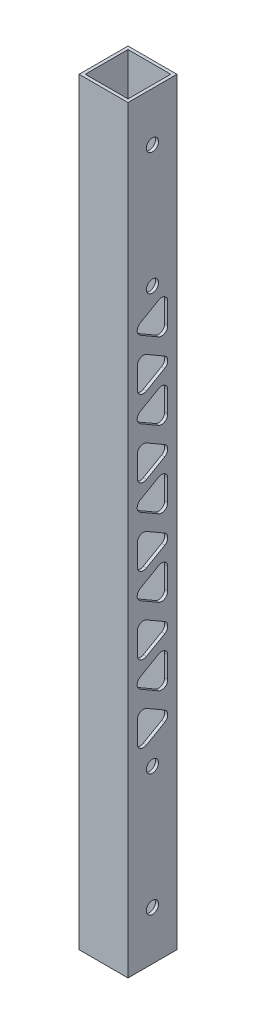
SolidWorks part; units mm, degrees
material "6061 Alloy"
ref_plane "Front Plane" through (0, 0, 0) normal (0, 0, 1) x (1, 0, 0)
ref_plane "Top Plane" through (0, 0, 0) normal (0, 1, 0) x (1, 0, 0)
ref_plane "Right Plane" through (0, 0, 0) normal (1, 0, 0) x (0, 0, -1)
sketch "Sketch1" plane through (0, 0, 0) normal (0, 1, 0) x (1, 0, 0)
  line L0 (-25.4, -25.4) -> (25.4, 25.4) construction
  line L1 (-25.4, 25.4) -> (25.4, 25.4)
  line L2 (-25.4, 25.4) -> (-25.4, -25.4)
  line L3 (-25.4, -25.4) -> (25.4, -25.4)
  line L4 (25.4, 25.4) -> (25.4, -25.4)
  line L5 (22.225, -22.225) -> (-22.225, 22.225) construction
  line L6 (-22.225, 22.225) -> (22.1918, 22.225)
  line L7 (-22.225, 22.225) -> (-22.225, -22.1918)
  line L8 (-22.225, -22.1918) -> (22.1918, -22.1918)
  line L9 (22.1918, 22.225) -> (22.1918, -22.1918)
  point P7 (0, 0)
  point P10 (0, 0)
  point P14 (0, 0)
  dimension "D1" = 50.8
  dimension "D2" = 3.175
  dimension "D3" = 3.175
extrude "Boss-Extrude1" add sketch "Sketch1" along normal blind 787.4
sketch "Sketch2" plane through (-25.4, 0, 0) normal (-1, 0, 0) x (0, 0, 1)
  line L0 (25.4, 393.7) -> (-25.4, 393.7) construction
  line L1 (25.4, 787.4) -> (25.4, 0) construction
  line L2 (-25.4, 787.4) -> (-25.4, 0) construction
  line L3 (0, 50.8) -> (0, 736.6) construction
  line L4 (0, 609.6) -> (0, 177.8) construction
  circle A0 centre (0, 50.8) radius 6.35
  circle A1 centre (0, 177.8) radius 6.35
  circle A2 centre (0, 609.6) radius 6.35
  circle A3 centre (0, 736.6) radius 6.35
  point P10 (0, 393.7)
  point P13 (0, 393.7)
  dimension "D3" = 12.7
extrude "Cut-Extrude1" cut sketch "Sketch2" against normal through all
sketch "Sketch3" plane through (-25.4, 0, 0) normal (-1, 0, 0) x (0, 0, 1)
  line L0 (15.7359, 216.4425) -> (15.7359, 861.9822) construction
  line L1 (-12.7, 210.9432) -> (6.2109, 200.025)
  line L2 (15.7359, 205.5243) -> (15.7359, 227.3607)
  line L3 (6.2109, 232.86) -> (-12.7, 221.9417)
  line L4 (12.7, 264.382) -> (-6.35, 275.3805)
  line L5 (-15.875, 269.8813) -> (-15.875, 247.8842)
  line L6 (-6.35, 242.385) -> (12.7, 253.3835)
  line L7 (-25.4, 787.4) -> (-25.4, 0) construction
  line L8 (25.4, 787.4) -> (25.4, 0) construction
  line L9 (-25.4, 393.7) -> (25.4, 393.7) construction
  line L10 (-6.35, 177.8) -> (6.35, 177.8) construction
  line L11 (-12.7, 290.5293) -> (6.2109, 279.6111)
  line L12 (15.7359, 285.1104) -> (15.7359, 306.9468)
  line L13 (6.2109, 312.4461) -> (-12.7, 301.5279)
  line L14 (12.7, 343.9681) -> (-6.35, 354.9667)
  line L15 (-15.875, 349.4674) -> (-15.875, 327.4704)
  line L16 (-6.35, 321.9711) -> (12.7, 332.9696)
  line L17 (-12.7, 370.1155) -> (6.2109, 359.1972)
  line L18 (15.7359, 364.6965) -> (15.7359, 386.5329)
  line L19 (6.2109, 392.0322) -> (-12.7, 381.114)
  line L20 (12.7, 423.5542) -> (-6.35, 434.5528)
  line L21 (-15.875, 429.0535) -> (-15.875, 407.0565)
  line L22 (-6.35, 401.5572) -> (12.7, 412.5557)
  line L23 (-12.7, 449.7016) -> (6.2109, 438.7833)
  line L24 (15.7359, 444.2826) -> (15.7359, 466.1191)
  line L25 (6.2109, 471.6183) -> (-12.7, 460.7001)
  line L26 (12.7, 503.1404) -> (-6.35, 514.1389)
  line L27 (-15.875, 508.6396) -> (-15.875, 486.6426)
  line L28 (-6.35, 481.1433) -> (12.7, 492.1418)
  line L29 (-12.7, 529.2877) -> (6.2109, 518.3695)
  line L30 (15.7359, 523.8687) -> (15.7359, 545.7052)
  line L31 (6.2109, 551.2044) -> (-12.7, 540.2862)
  line L32 (12.7, 582.7265) -> (-6.35, 593.725)
  line L33 (-15.875, 588.2257) -> (-15.875, 566.2287)
  line L34 (-6.35, 560.7294) -> (12.7, 571.728)
  circle A0 centre (3.0823, 216.4425) radius 12.6536 construction
  circle A1 centre (-3.175, 258.8828) radius 12.7 construction
  arc A2 (-12.7, 210.9432) -> (-12.7, 221.9417) centre (-9.525, 216.4425) cw
  arc A3 (15.7359, 227.3607) -> (6.2109, 232.86) centre (9.3859, 227.3607) ccw
  arc A4 (6.2109, 200.025) -> (15.7359, 205.5243) centre (9.3859, 205.5243) ccw
  arc A5 (12.7, 264.382) -> (12.7, 253.3835) centre (9.525, 258.8828) cw
  arc A6 (-15.875, 247.8842) -> (-6.35, 242.385) centre (-9.525, 247.8842) ccw
  arc A7 (-6.35, 275.3805) -> (-15.875, 269.8813) centre (-9.525, 269.8813) ccw
  circle A11 centre (0, 177.8) radius 6.35 construction
  arc A12 (6.2109, 279.6111) -> (15.7359, 285.1104) centre (9.3859, 285.1104) ccw
  arc A13 (-12.7, 290.5293) -> (-12.7, 301.5279) centre (-9.525, 296.0286) cw
  arc A14 (15.7359, 306.9468) -> (6.2109, 312.4461) centre (9.3859, 306.9468) ccw
  arc A15 (-6.35, 354.9667) -> (-15.875, 349.4674) centre (-9.525, 349.4674) ccw
  arc A16 (12.7, 343.9681) -> (12.7, 332.9696) centre (9.525, 338.4689) cw
  arc A17 (-15.875, 327.4704) -> (-6.35, 321.9711) centre (-9.525, 327.4704) ccw
  arc A18 (6.2109, 359.1972) -> (15.7359, 364.6965) centre (9.3859, 364.6965) ccw
  arc A19 (-12.7, 370.1155) -> (-12.7, 381.114) centre (-9.525, 375.6147) cw
  arc A20 (15.7359, 386.5329) -> (6.2109, 392.0322) centre (9.3859, 386.5329) ccw
  arc A21 (-6.35, 434.5528) -> (-15.875, 429.0535) centre (-9.525, 429.0535) ccw
  arc A22 (12.7, 423.5542) -> (12.7, 412.5557) centre (9.525, 418.055) cw
  arc A23 (-15.875, 407.0565) -> (-6.35, 401.5572) centre (-9.525, 407.0565) ccw
  arc A24 (6.2109, 438.7833) -> (15.7359, 444.2826) centre (9.3859, 444.2826) ccw
  arc A25 (-12.7, 449.7016) -> (-12.7, 460.7001) centre (-9.525, 455.2008) cw
  arc A26 (15.7359, 466.1191) -> (6.2109, 471.6183) centre (9.3859, 466.1191) ccw
  arc A27 (-6.35, 514.1389) -> (-15.875, 508.6396) centre (-9.525, 508.6396) ccw
  arc A28 (12.7, 503.1404) -> (12.7, 492.1418) centre (9.525, 497.6411) cw
  arc A29 (-15.875, 486.6426) -> (-6.35, 481.1433) centre (-9.525, 486.6426) ccw
  arc A30 (6.2109, 518.3695) -> (15.7359, 523.8687) centre (9.3859, 523.8687) ccw
  arc A31 (-12.7, 529.2877) -> (-12.7, 540.2862) centre (-9.525, 534.7869) cw
  arc A32 (15.7359, 545.7052) -> (6.2109, 551.2044) centre (9.3859, 545.7052) ccw
  arc A33 (-6.35, 593.725) -> (-15.875, 588.2257) centre (-9.525, 588.2257) ccw
  arc A34 (12.7, 582.7265) -> (12.7, 571.728) centre (9.525, 577.2272) cw
  arc A35 (-15.875, 566.2287) -> (-6.35, 560.7294) centre (-9.525, 566.2287) ccw
  circle A36 centre (0, 609.6) radius 6.35 construction
  point P16 (15.7359, 238.3592)
  point P23 (22.225, 258.8828)
  point P28 (-9.525, 559.6331)
  point P29 (-15.875, 216.4425)
  point P34 (15.875, 258.8828)
  point P37 (-6.35, 177.8)
  dimension "D1" = 6.35
  dimension "D2" = 6.35
  dimension "D5" = 9.525
  dimension "D8" = 5
  dimension "D9" = 15.875
  dimension "D4" = 22.225
  dimension "D3" = 9.525
  dimension "D6" = 9.525
  dimension "D7" = 9.525
extrude "Cut-Extrude2" cut sketch "Sketch3" against normal blind 76.2
equation "\"D1@Boss-Extrude1\"=\"HoleDist\"+4"
